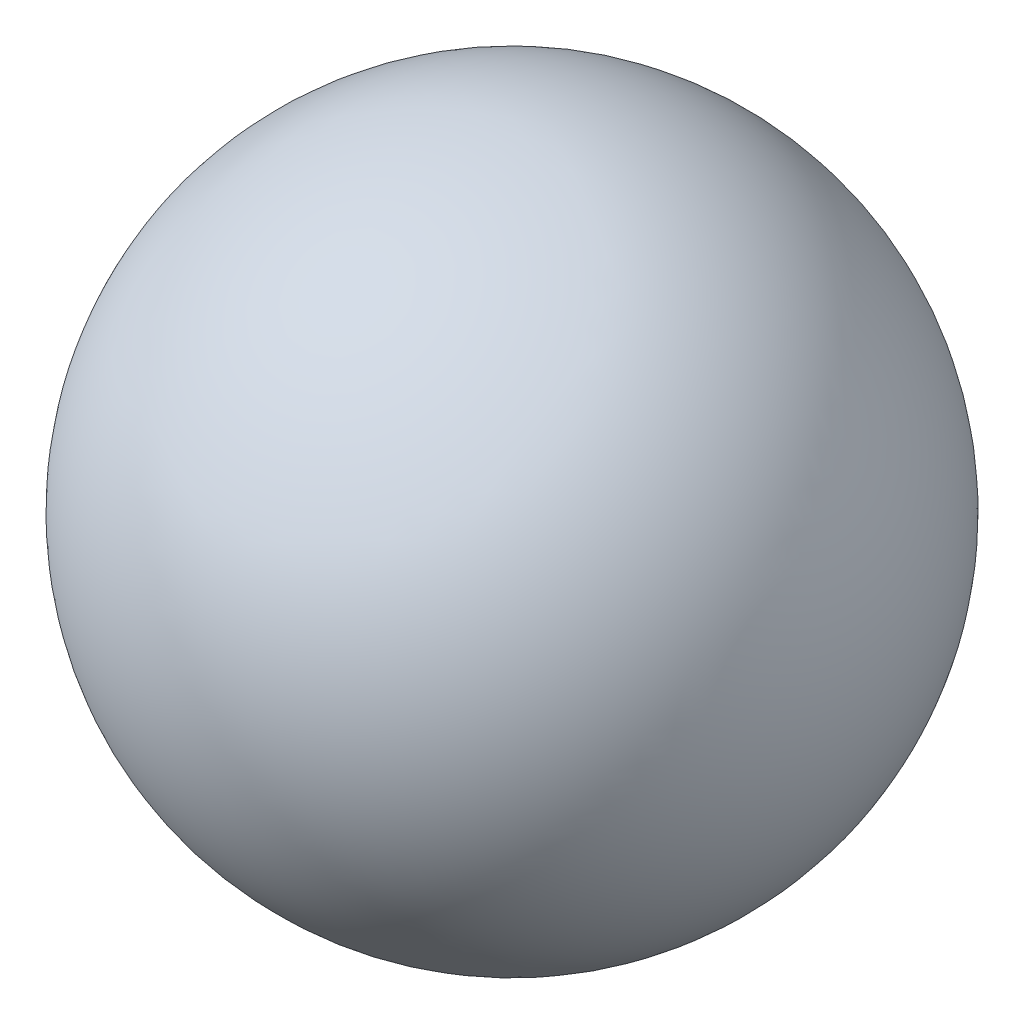
SolidWorks part; units mm, degrees
ref_plane "Front Plane" through (0, 0, 0) normal (0, 0, 1) x (1, 0, 0)
ref_plane "Top Plane" through (0, 0, 0) normal (0, 1, 0) x (1, 0, 0)
ref_plane "Right Plane" through (0, 0, 0) normal (1, 0, 0) x (0, 0, -1)
sketch "Sketch1" plane through (0, 0, 0) normal (0, 1, 0) x (1, 0, 0)
  line L0 (-12.5, 0) -> (12.5, 0)
  arc A0 (-12.5, 0) -> (12.5, 0) centre (0, 0) ccw
  dimension "D1" = 25
revolve "Revolve1" add sketch "Sketch1" angle 360 about L0
